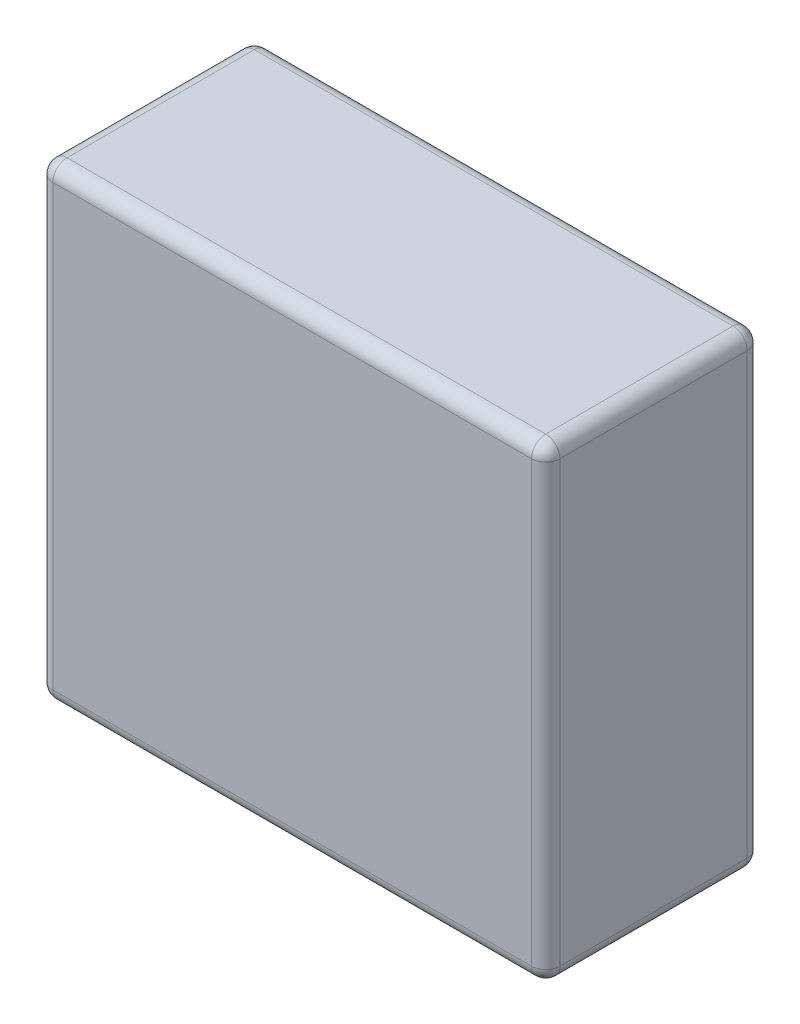
SolidWorks part; units mm, degrees
ref_plane "Front Plane" through (0, 0, 0) normal (0, 0, 1) x (1, 0, 0)
ref_plane "Top Plane" through (0, 0, 0) normal (0, 1, 0) x (1, 0, 0)
ref_plane "Right Plane" through (0, 0, 0) normal (1, 0, 0) x (0, 0, -1)
sketch "Sketch2" plane through (0, 0, 0) normal (1, 0, 0) x (0, 0, -1)
  line L1 (0, 0) -> (77, 0)
  line L2 (0, 0) -> (0, 167)
  line L3 (0, 167) -> (77, 167)
  line L4 (77, 0) -> (77, 167)
extrude "Boss-Extrude1" add sketch "Sketch2" along normal blind 181
fillet "Fillet1" radius 5.08 12 edges at (0, 0, -38.5) (90.5, 0, 0) (90.5, 0, -77) (181, 0, -38.5) (181, 83.5, -77) (181, 167, -38.5) (181, 83.5, 0) (90.5, 167, -77) (0, 83.5, -77) (0, 83.5, 0) (0, 167, -38.5) (90.5, 167, 0)
